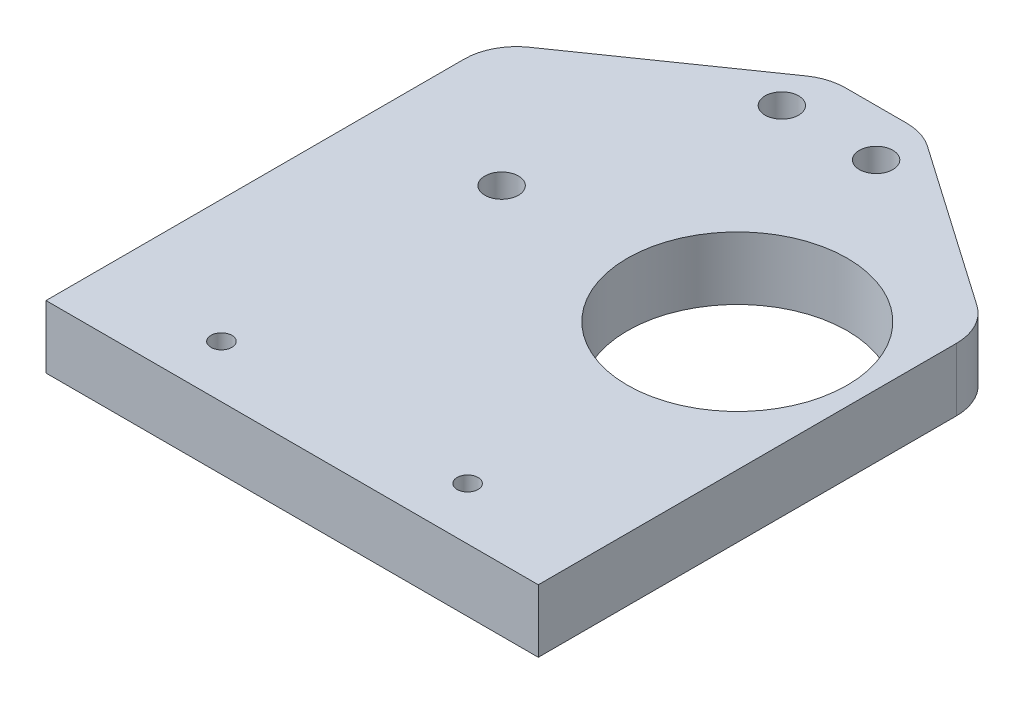
SolidWorks part; units mm, degrees
ref_plane "Front Plane" through (0, 0, 0) normal (0, 0, 1) x (1, 0, 0)
ref_plane "Top Plane" through (0, 0, 0) normal (0, 1, 0) x (1, 0, 0)
ref_plane "Right Plane" through (0, 0, 0) normal (1, 0, 0) x (0, 0, -1)
sketch "Sketch1" plane through (0, 0, 0) normal (0, 1, 0) x (1, 0, 0)
  line L0 (0, 0) -> (0, 45.75) construction
  line L1 (23.5, 45.75) -> (-23.5, 45.75)
  line L2 (-23.5, 45.75) -> (-23.5, 0)
  line L3 (-23.5, 0) -> (23.5, 0)
  line L4 (23.5, 45.75) -> (23.5, 0)
  circle A0 centre (-4.5, 41.25) radius 1.6
  circle A1 centre (-11.25, 21.25) radius 1.6
  circle A2 centre (11.25, 21.25) radius 1.6
  circle A3 centre (4.5, 41.25) radius 1.6
  dimension "D3" = 3.2
  dimension "D4" = 3.2
  dimension "D1" = 23.5
  dimension "D2" = 45.75
  dimension "D5" = 9
  dimension "D6" = 11.25
  dimension "D7" = 4.5
  dimension "D8" = 20
  dimension "D9" = 6.75
  dimension "D10" = 12.25
extrude "Boss-Extrude1" add sketch "Sketch1" along normal blind 6
sketch "Sketch2" plane through (0, 6, 0) normal (0, 1, 0) x (1, 0, 0)
  line L0 (23.5, 32.53) -> (4.5, 45.75)
  line L1 (23.5, 0) -> (23.5, 45.75) construction
  line L2 (23.5, 45.75) -> (-23.5, 45.75) construction
  line L3 (-23.5, 32.53) -> (-4.5, 45.75)
  line L4 (-23.5, 45.75) -> (-23.5, 0) construction
  line L5 (-23.5, 32.53) -> (-23.5, 45.75)
  line L6 (-23.5, 45.75) -> (-4.5, 45.75)
  line L7 (4.5, 45.75) -> (23.5, 45.75)
  line L8 (23.5, 45.75) -> (23.5, 32.53)
  dimension "D1" = 13.22
  dimension "D2" = 13.22
  dimension "D3" = 19
  dimension "D4" = 19
extrude "Cut-Extrude1" cut sketch "Sketch2" against normal through all
fillet "Fillet1" radius 5 4 edges at (23.5, 3, -32.53) (4.5, 3, -45.75) (-4.5, 3, -45.75) (-23.5, 3, -32.53)
sketch "Sketch3" plane through (0, 0, 0) normal (0, -1, 0) x (1, 0, 0)
  circle A0 centre (11.25, -21.25) radius 10.5
  dimension "D1" = 21
extrude "Cut-Extrude2" cut sketch "Sketch3" against normal through all
sketch "Sketch4" plane through (0, 0, 0) normal (0, 0, 1) x (1, 0, 0)
  line L1 (-23.5, 6) -> (23.5, 6)
  line L2 (-23.5, 6) -> (-23.5, 0)
  line L3 (-23.5, 0) -> (23.5, 0)
  line L4 (23.5, 6) -> (23.5, 0)
extrude "Boss-Extrude2" add sketch "Sketch4" along normal blind 10
sketch "Sketch6" plane through (0, 6, 0) normal (0, 1, 0) x (1, 0, 0)
  line L0 (-23.5, 29.9177) -> (-23.5, -10) construction
  line L1 (23.5, -10) -> (23.5, 29.9177) construction
  line L2 (23.5, -10) -> (-23.5, -10) construction
  circle A0 centre (-11.75, -5) radius 1
  circle A1 centre (11.75, -5) radius 1
  dimension "D1" = 2
  dimension "D2" = 2
  dimension "D3" = 11.75
  dimension "D4" = 11.75
  dimension "D5" = 5
  dimension "D6" = 5
extrude "Cut-Extrude3" cut sketch "Sketch6" against normal through all
